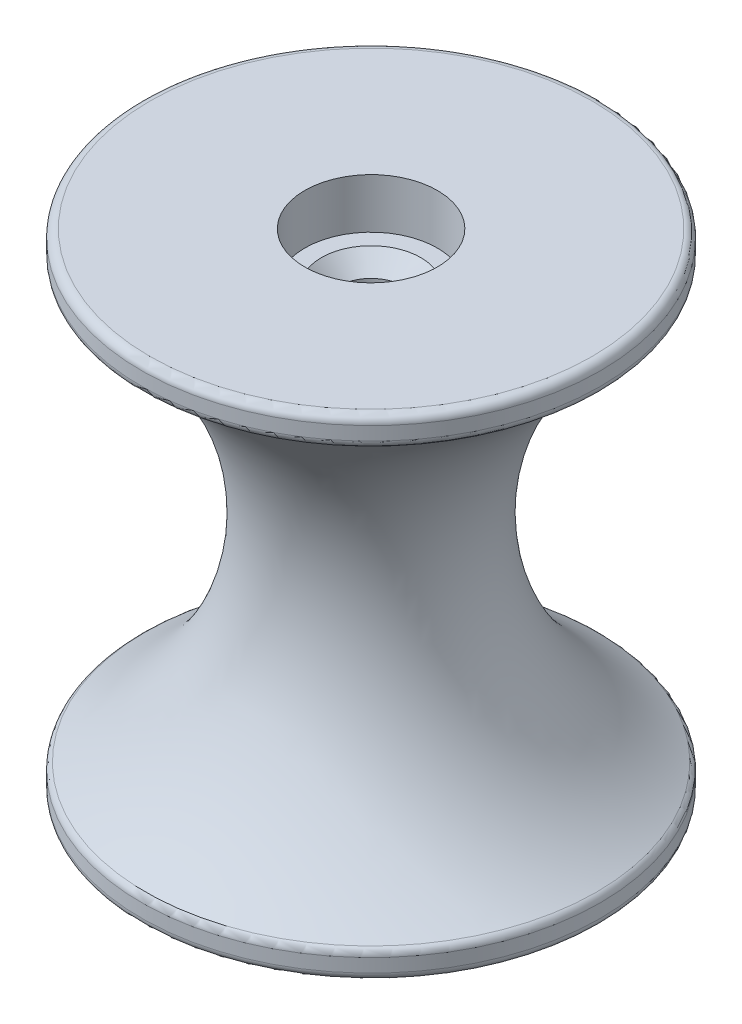
SolidWorks part; units mm, degrees
ref_plane "Front" through (0, 0, 0) normal (0, 0, 1) x (1, 0, 0)
ref_plane "Top" through (0, 0, 0) normal (0, 1, 0) x (1, 0, 0)
ref_plane "Right" through (0, 0, 0) normal (1, 0, 0) x (0, 0, -1)
sketch "Sketch1" plane through (0, 0, 0) normal (0, 0, 1) x (1, 0, 0)
  line L0 (-21.9693, 23.4903) -> (0, 23.4903)
  line L1 (-21.9693, 23.4903) -> (-21.9693, 20.9503)
  line L2 (0, 23.4903) -> (0, -23.4903)
  line L3 (-21.9693, -23.4903) -> (0, -23.4903)
  line L4 (-21.9693, 23.4903) -> (0, -23.4903) construction
  line L5 (0, 23.4903) -> (-21.9693, -23.4903) construction
  line L6 (-6.35, 23.4903) -> (-6.35, 18.7151)
  line L7 (-6.35, -23.4903) -> (-6.35, -18.7151)
  line L8 (-21.9693, -20.9503) -> (-21.9693, -23.4903)
  line L9 (-6.35, -18.7151) -> (-6.35, -23.4903)
  line L11 (-6.35, -23.4903) -> (-6.35, -18.7151)
  line L12 (0, 0) -> (-21.9693, 0) construction
  line L13 (-6.35, 18.7151) -> (-4.7625, 18.7151)
  line L14 (-6.35, -18.7151) -> (-4.7625, -18.7151)
  line L15 (-4.7625, 18.7151) -> (-3.175, 17.1276)
  line L16 (-4.7625, -18.7151) -> (-3.175, -17.1276)
  line L17 (-3.175, 17.1276) -> (-3.175, -17.1276)
  arc A0 (-21.9693, 20.9503) -> (-21.9693, -20.9503) centre (-35.0021, 0) cw
  circle A1 centre (-33.8134, 0) radius 24.0665
  point P1 (-10.9847, 0)
  point P20 (-3.175, 0)
  point P26 (-10.3289, 0)
  dimension "D7" = 48.133
  dimension "D8" = 24.6732
  dimension "D1" = 3.175
  dimension "D2" = 1.5875
  dimension "D3" = 6.35
  dimension "D4" = 4.7752
  dimension "D5" = 46.9805
  dimension "D6" = 1.5875
  dimension "D9" = 2.54
  dimension "D10" = 2.54
  dimension "D11" = 21.9693
  dimension "D12" = 33.8134
revolve "Revolve1" add sketch "Sketch1" angle 360 about L2
fillet "Fillet1" radius 0.7937 4 edges at (-21.9693, -23.4903, 0) (-21.9693, 23.4903, 0) (-21.9693, 20.9503, 0) (-21.9693, -20.9503, 0)
